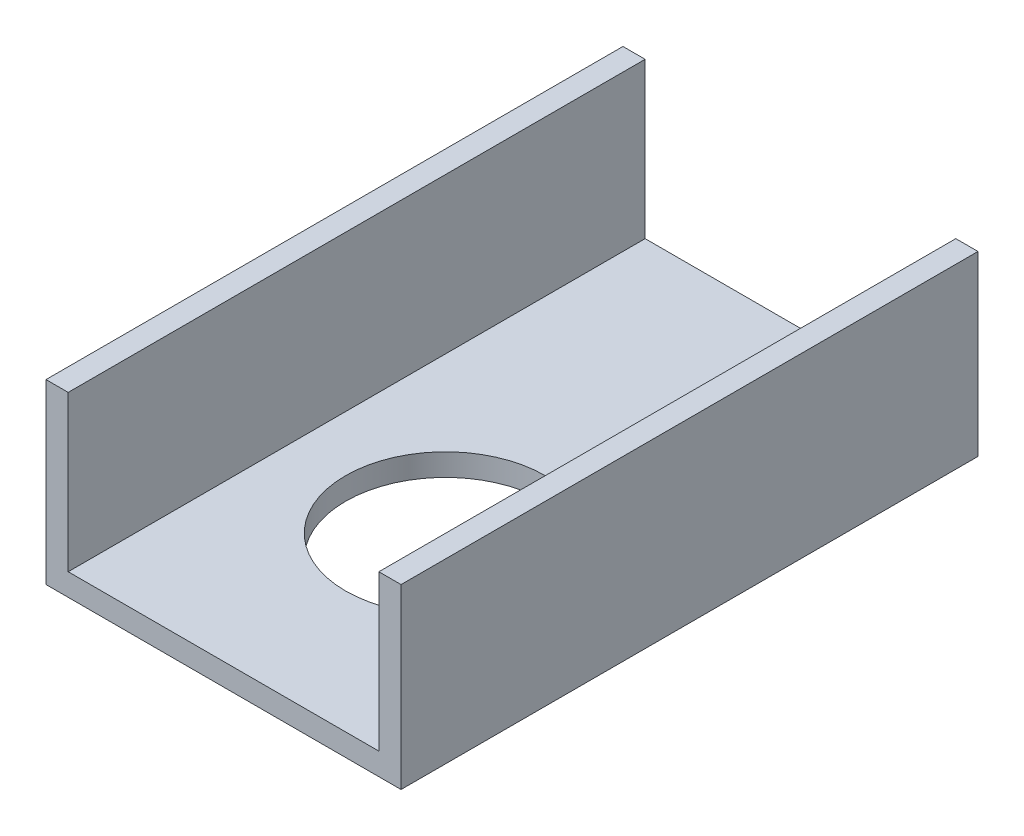
SolidWorks part; units mm, degrees
material "6063-T6"
ref_plane "Front" through (0, 0, 0) normal (0, 0, 1) x (1, 0, 0)
ref_plane "Top" through (0, 0, 0) normal (0, 1, 0) x (1, 0, 0)
ref_plane "Right" through (0, 0, 0) normal (1, 0, 0) x (0, 0, -1)
sketch "Sketch1" plane through (0, 0, 0) normal (0, 0, 1) x (1, 0, 0)
  line L0 (47.625, 3.175) -> (47.625, 25.4)
  line L1 (0, 0) -> (50.8, 0)
  line L2 (0, 0) -> (0, 25.4)
  line L4 (50.8, 0) -> (50.8, 25.4)
  line L5 (3.175, 3.175) -> (47.625, 3.175)
  line L6 (3.175, 3.175) -> (3.175, 25.4)
  line L7 (50.8, 25.4) -> (47.625, 25.4)
  line L8 (0, 25.4) -> (3.175, 25.4)
  dimension "D1" = 25.4
  dimension "D2" = 50.8
  dimension "D3" = 3.175
extrude "Boss-Extrude1" add sketch "Sketch1" along normal blind 82.55
sketch "Sketch2" plane through (0, 0, 0) normal (0, -1, 0) x (1, 0, 0)
  line L0 (25.4, 50.8) -> (25.4, 82.55) construction
  line L1 (0, 82.55) -> (50.8, 82.55) construction
  circle A0 centre (25.4, 50.8) radius 14.2875
  dimension "D1" = 28.575
  dimension "D2" = 31.75
extrude "Cut-Extrude1" cut sketch "Sketch2" against normal up to next
sketch "Sketch3" plane through (0, 3.175, 0) normal (0, 1, 0) x (1, 0, 0)
  line L1 (44.45, -22.225) -> (47.625, -22.225)
  line L2 (44.45, -22.225) -> (44.45, 0)
  line L3 (44.45, 0) -> (47.625, 0)
  line L4 (47.625, -22.225) -> (47.625, 0)
  line L5 (44.45, -22.225) -> (47.625, 0) construction
  line L6 (44.45, 0) -> (47.625, -22.225) construction
  line L8 (47.625, -82.55) -> (47.625, 0) construction
  line L9 (47.625, 0) -> (3.175, 0) construction
  point P4 (46.0375, -11.1125)
  dimension "D1" = 22.225
  dimension "D2" = 3.175
extrude "Cut-Extrude2" cut sketch "Sketch3" against normal up to next
